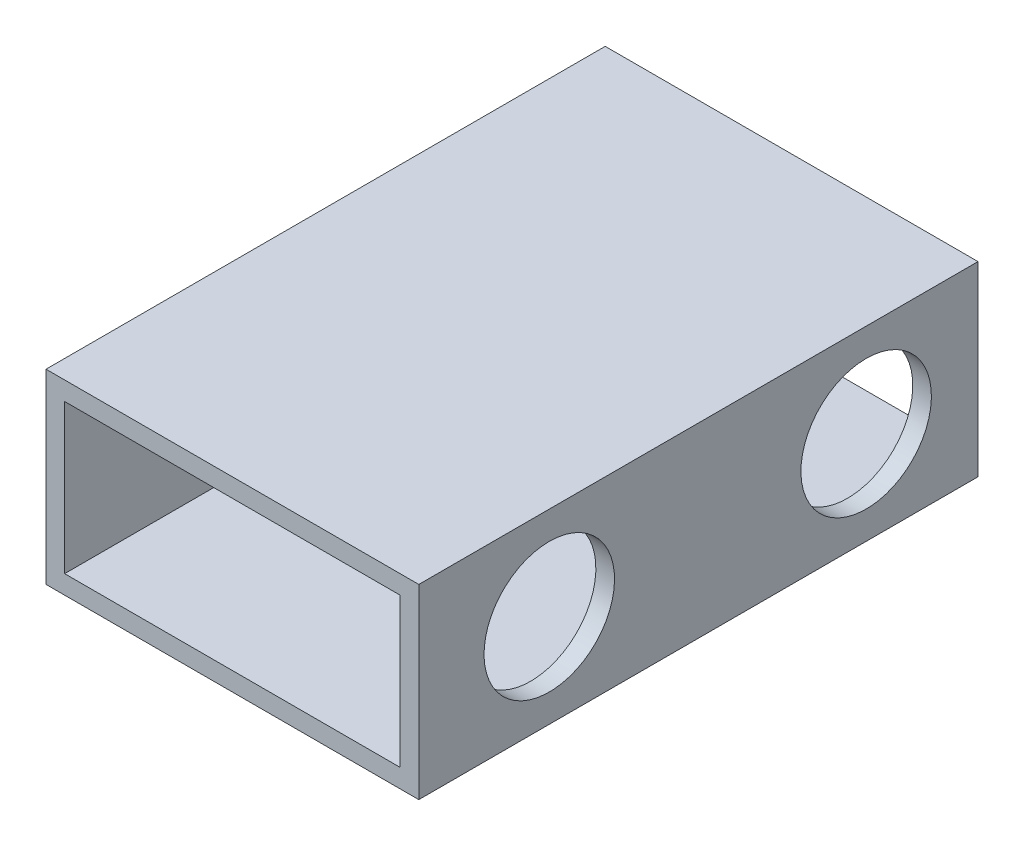
SolidWorks part; units mm, degrees
material "6063-O"
ref_plane "前视基准面" through (0, 0, 0) normal (0, 0, 1) x (1, 0, 0)
ref_plane "上视基准面" through (0, 0, 0) normal (0, 1, 0) x (1, 0, 0)
ref_plane "右视基准面" through (0, 0, 0) normal (1, 0, 0) x (0, 0, -1)
other "Configuration Table"
sketch "草图1" plane through (0, 0, 0) normal (0, 0, 1) x (1, 0, 0)
  line L1 (9.2129, 36.3977) -> (29.2129, 36.3977)
  line L2 (9.2129, 36.3977) -> (9.2129, 26.3977)
  line L3 (9.2129, 26.3977) -> (29.2129, 26.3977)
  line L4 (29.2129, 36.3977) -> (29.2129, 26.3977)
  line L5 (9.2129, 36.3977) -> (29.2129, 26.3977) construction
  line L6 (9.2129, 26.3977) -> (29.2129, 36.3977) construction
  point P4 (19.2129, 31.3977)
  dimension "D1" = 20
  dimension "D2" = 10
extrude "拉伸-薄壁1" add sketch "草图1" along normal blind 30 thin
sketch "草图2" plane through (29.2129, 0, 0) normal (1, 0, 0) x (0, 0, -1)
  line L0 (-30, 31.3977) -> (0, 31.3977) construction
  line L1 (-30, 26.3977) -> (-30, 36.3977) construction
  line L2 (0, 26.3977) -> (0, 36.3977) construction
  circle A0 centre (-23, 31.3977) radius 1.5
  circle A1 centre (-6, 31.3977) radius 1.5
  dimension "D1" = 3
  dimension "D2" = 6
  dimension "D3" = 17
extrude "切除-拉伸1" cut sketch "草图2" against normal blind 20
sketch "草图3" plane through (29.2129, 0, 0) normal (1, 0, 0) x (0, 0, -1)
  circle A0 centre (-23, 31.3977) radius 3.5
  circle A1 centre (-6, 31.3977) radius 3.5
  dimension "D1" = 7
extrude "切除-拉伸2" cut sketch "草图3" against normal blind 5
